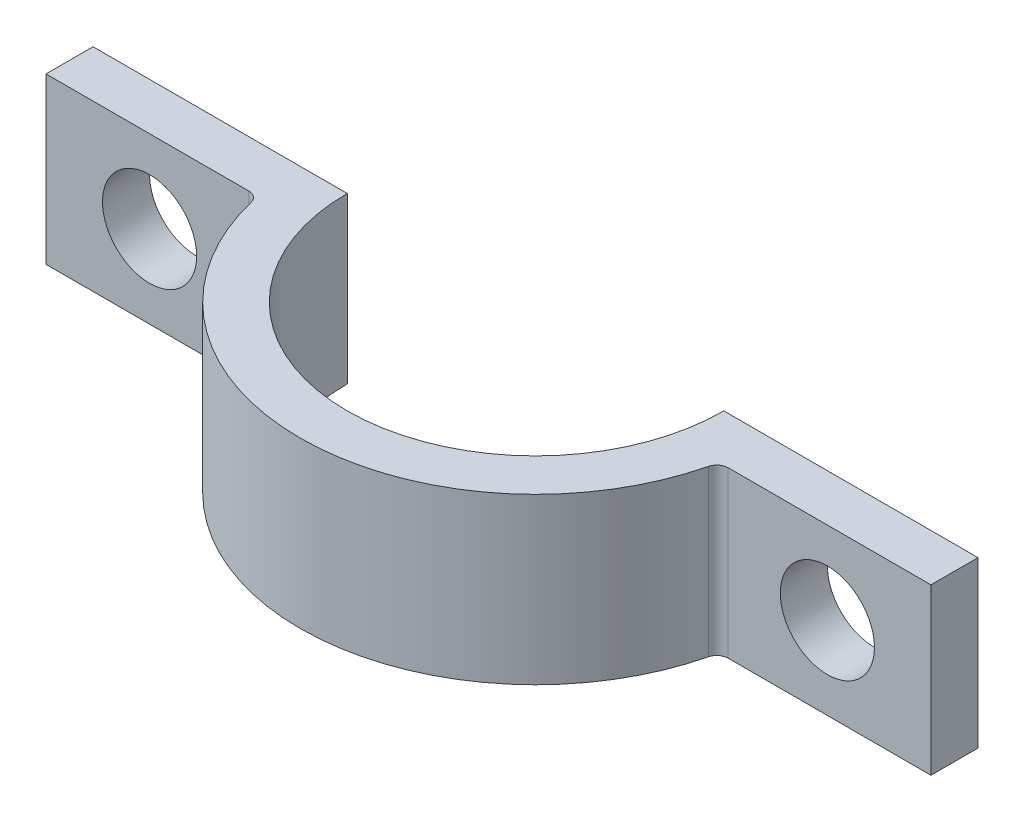
SolidWorks part; units mm, degrees
material "6061-T6 (SS)"
ref_plane "X-Y Datum" through (0, 0, 0) normal (0, 0, 1) x (1, 0, 0)
ref_plane "X-Z Datum" through (0, 0, 0) normal (0, 1, 0) x (1, 0, 0)
ref_plane "Y-Z Datum" through (0, 0, 0) normal (1, 0, 0) x (0, 0, -1)
sketch "Sketch1" plane through (0, 0, 0) normal (0, 1, 0) x (1, 0, 0)
  line L0 (-12.7, 0) -> (-29.845, 0)
  line L1 (-29.845, 0) -> (-29.845, -3.175)
  line L2 (-29.845, -3.175) -> (-16.1645, -3.175)
  line L3 (12.7, 0) -> (29.845, 0)
  line L4 (29.845, 0) -> (29.845, -3.175)
  line L5 (29.845, -3.175) -> (16.1645, -3.175)
  arc A0 (-12.7, 0) -> (12.7, 0) centre (0, 0) ccw
  arc A1 (-15.4241, -3.7567) -> (15.4241, -3.7567) centre (0, 0) ccw
  arc A2 (15.4241, -3.7567) -> (16.1645, -3.175) centre (16.1645, -3.937) cw
  arc A3 (-15.875, 0) -> (15.875, 0) centre (0, 0) ccw construction
  arc A4 (-15.4241, -3.7567) -> (-16.1645, -3.175) centre (-16.1645, -3.937) ccw
  dimension "D1" = 3.175
  dimension "D3" = 12.7
  dimension "D5" = 0.762
  dimension "D2" = 3.175
  dimension "D4" = 59.69
extrude "Boss-Extrude1" add sketch "Sketch1" along normal mid plane 11.1252
sketch "Sketch2" plane through (0, 0, 3.175) normal (0, 0, 1) x (1, 0, 0)
  line L0 (-29.845, 5.5626) -> (-16.1645, 5.5626) construction
  line L1 (-22.86, 0) -> (22.86, 0) construction
  circle A0 centre (-22.86, 0) radius 3.175
  circle A1 centre (22.86, 0) radius 3.175
  point P6 (0, 0)
  dimension "D1" = 5.5626
  dimension "D3" = 6.35
  dimension "D2" = 22.86
extrude "Cut-Extrude1" cut sketch "Sketch2" against normal through all
fillet "Fillet1" [suppressed] radius 3.81
fillet "Fillet2" [suppressed] radius 0.254
